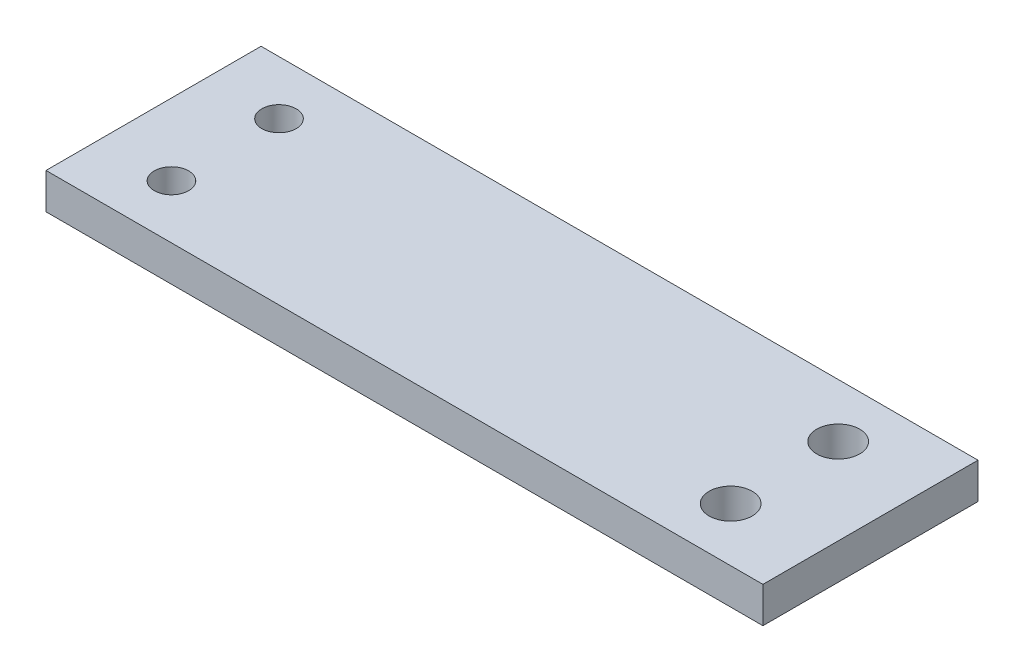
SolidWorks part; units mm, degrees
ref_plane "Ebene vorne" through (0, 0, 0) normal (0, 0, 1) x (1, 0, 0)
ref_plane "Ebene oben" through (0, 0, 0) normal (0, 1, 0) x (1, 0, 0)
ref_plane "Ebene rechts" through (0, 0, 0) normal (1, 0, 0) x (0, 0, -1)
sketch "Skizze1" plane through (0, 0, 0) normal (0, 0, 1) x (1, 0, 0)
  line L0 (-35, 16) -> (65, 16)
  line L2 (65, 16) -> (65, 21)
  line L3 (65, 21) -> (-35, 21)
  line L4 (-35, 21) -> (-35, 16)
sketch "Skizze3" plane through (0, 0, 0) normal (0, 0, 1) x (1, 0, 0)
  line L1 (-35, 21) -> (65, 21)
  line L2 (-35, 21) -> (-35, 16)
  line L3 (-35, 16) -> (65, 16)
  line L4 (65, 21) -> (65, 16)
sketch "Skizze4" plane through (0, 0, 0) normal (1, 0, 0) x (0, 0, -1)
  line L0 (15, 0) -> (-15, 0)
  point P8 (0, 0)
extrude "Aufsatz-Linear austragen1" add sketch "Skizze3" along normal up to vertex (15 mm away) and the other way up to vertex (15 mm away) up to point (0, 0, 15) other way up to point (0, 0, -15)
sketch "Skizze7" plane through (0, 0, 0) normal (0, 1, 0) x (1, 0, 0)
  line L1 (0, 0) -> (30.9843, 0) construction
  line L4 (-65, -15) -> (65, -15)
  line L5 (-65, -15) -> (-65, 15)
  line L6 (-65, 15) -> (65, 15)
  line L7 (65, -15) -> (65, 15)
  line L8 (-65, -15) -> (65, 15) construction
  line L9 (-65, 15) -> (65, -15) construction
  circle A0 centre (53, -7.5) radius 1.65
  circle A1 centre (53, 7.5) radius 1.65
  circle A2 centre (-53, 7.5) radius 1.65
  circle A3 centre (-53, -7.5) radius 1.65
  point P8 (0, 0)
sketch "Skizze8" plane through (0, 0, 0) normal (0, 1, 0) x (1, 0, 0)
  circle A0 centre (53, 7.5) radius 3
  circle A1 centre (53, -7.5) radius 3
  circle A4 centre (53, -7.5) radius 1.65 construction
  circle A5 centre (53, 7.5) radius 1.65 construction
  dimension "D1" = 6
  dimension "D2" = 6
extrude "Schnitt-Linear austragen1" cut sketch "Skizze8" along normal up to surface (21 mm away) up to face at (15, 21, 0)
sketch "Skizze9" plane through (0, 0, 0) normal (0, 1, 0) x (1, 0, 0)
  line L3 (0, 0) -> (-74.7932, 0) construction
  circle A0 centre (-25, 7.5) radius 3
  circle A1 centre (-25, -7.5) radius 3
sketch "Skizze10" plane through (0, 0, 0) normal (0, 1, 0) x (1, 0, 0)
  circle A0 centre (-25, 7.5) radius 2.4
  circle A1 centre (-25, -7.5) radius 2.4
  dimension "D1" = 4.8
  dimension "D2" = 4.8
extrude "Schnitt-Linear austragen2" cut sketch "Skizze10" along normal up to surface (21 mm away) up to face at (56, 21, -7.5)
